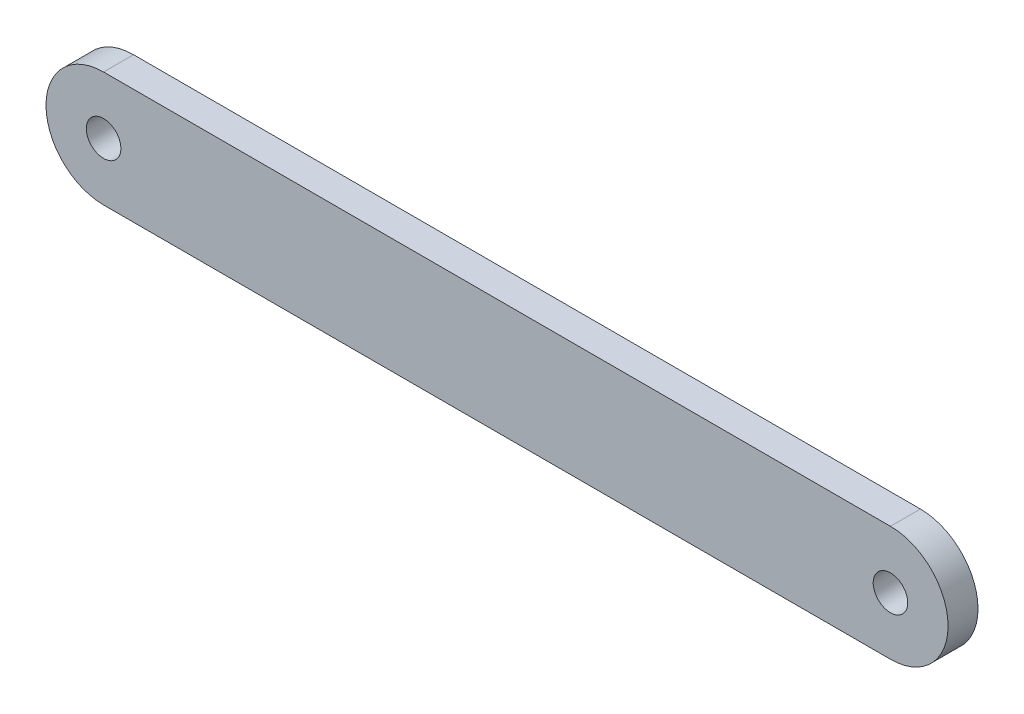
SolidWorks part; units mm, degrees
ref_plane "前基準面" through (0, 0, 0) normal (0, 0, 1) x (1, 0, 0)
ref_plane "上基準面" through (0, 0, 0) normal (0, 1, 0) x (1, 0, 0)
ref_plane "右基準面" through (0, 0, 0) normal (1, 0, 0) x (0, 0, -1)
sketch "草圖1" plane through (0, 0, 0) normal (0, 0, 1) x (1, 0, 0)
  line L0 (-17.08, 0) -> (17.08, 0) construction
  line L1 (-17.08, 2.5) -> (17.08, 2.5)
  line L2 (-17.08, -2.5) -> (17.08, -2.5)
  arc A0 (-17.08, 2.5) -> (-17.08, -2.5) centre (-17.08, 0) ccw
  arc A1 (17.08, -2.5) -> (17.08, 2.5) centre (17.08, 0) ccw
  circle A2 centre (-17.08, 0) radius 0.75
  circle A3 centre (17.08, 0) radius 0.75
  point P3 (0, 0)
  dimension "D2" = 2.5
  dimension "D3" = 1.5
  dimension "D1" = 34.16
extrude "填料-伸長1" add sketch "草圖1" along normal mid plane 1.3
